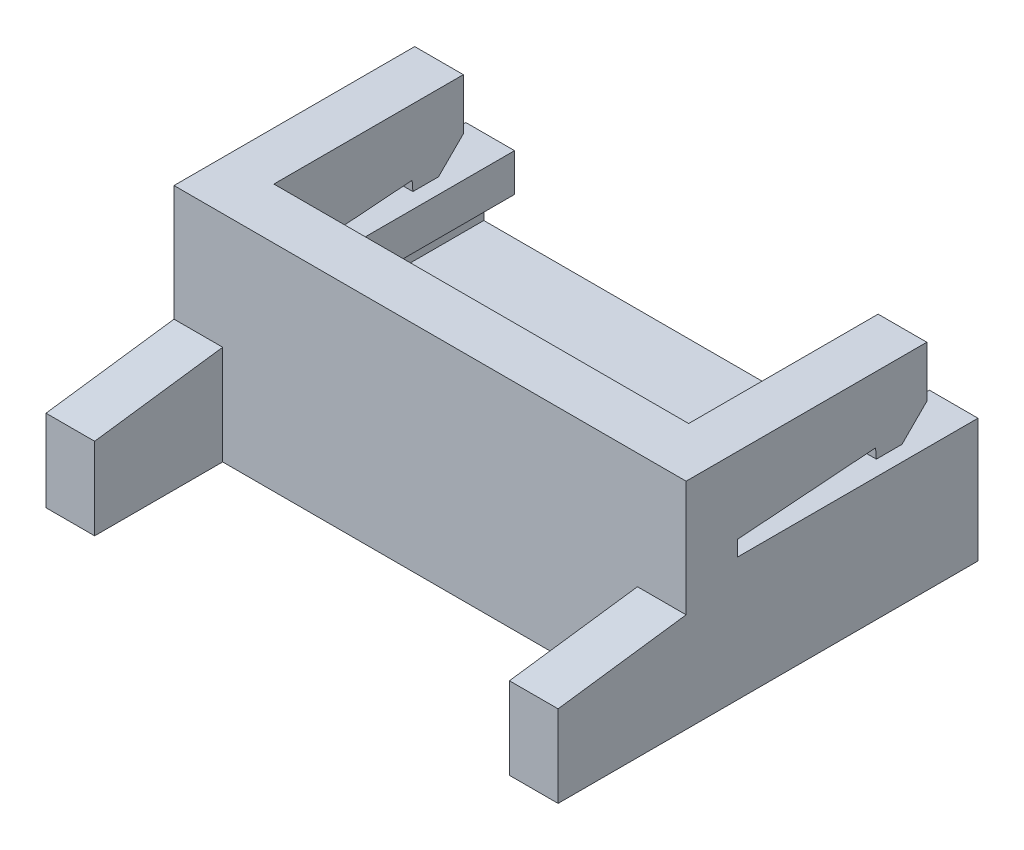
SolidWorks part; units mm, degrees
ref_plane "Front Plane" through (0, 0, 0) normal (0, 0, 1) x (1, 0, 0)
ref_plane "Top Plane" through (0, 0, 0) normal (0, 1, 0) x (1, 0, 0)
ref_plane "Right Plane" through (0, 0, 0) normal (1, 0, 0) x (0, 0, -1)
sketch "Sketch1" plane through (0, 0, 0) normal (0, 1, 0) x (1, 0, 0)
  line L1 (0, 0) -> (10, 0)
  line L2 (0, 0) -> (0, -8.2)
  line L3 (0, -8.2) -> (10, -8.2)
  line L4 (10, 0) -> (10, -8.2)
  dimension "D1" = 8.2
  dimension "D2" = 10
extrude "Boss-Extrude1" add sketch "Sketch1" along normal blind 4.2
sketch "Sketch2" plane through (0, 0, 0) normal (-1, 0, 0) x (0, 0, 1)
  line L0 (8.2, 4.2) -> (8.2, 1.6)
  line L1 (8.2, 4.2) -> (8.2, 0) construction
  line L2 (8.2, 1.6) -> (5.7, 1.94)
  line L3 (5.7, 1.94) -> (5.7, 4.2)
  line L4 (0, 4.2) -> (8.2, 4.2) construction
  line L5 (5.7, 4.2) -> (8.2, 4.2)
  line L6 (0, 0) -> (8.2, 0) construction
  dimension "D1" = 1.6
  dimension "D2" = 2.5
  dimension "D3" = 2.26
extrude "Cut-Extrude1" cut sketch "Sketch2" against normal up to surface (10 mm away) up to face at (10, 2.1, 4.1)
sketch "Sketch3" plane through (0, 0, 0) normal (-1, 0, 0) x (0, 0, 1)
  line L0 (0, 2.4148) -> (4.7, 2.4148)
  line L1 (0, 4.2) -> (0, 0) construction
  line L2 (4.7, 2.4148) -> (4.7, 2.7148)
  line L3 (4.7, 2.7148) -> (2, 2.9148)
  line L4 (2, 2.9148) -> (1.9852, 2.7148)
  line L5 (1.9852, 2.7148) -> (1.4852, 2.7148)
  line L6 (1.4852, 2.7148) -> (1, 3.2)
  line L7 (1, 3.2) -> (1, 4.2)
  line L8 (0, 4.2) -> (5.7, 4.2) construction
  line L9 (1, 4.2) -> (0, 4.2)
  line L10 (0, 4.2) -> (0, 2.4148)
  dimension "D1" = 1
  dimension "D2" = 4.7
  dimension "D3" = 0.3
  dimension "D4" = 0.5
  dimension "D5" = 45
  dimension "D6" = 0.3
  dimension "D7" = 2.7
  dimension "D8" = 0.5
  dimension "D9" = 1
extrude "Cut-Extrude2" cut sketch "Sketch3" against normal up to surface (10 mm away) up to face at (10, 1.99, 4.6333)
sketch "Sketch4" plane through (0, 0, 0) normal (0, 0, -1) x (-1, 0, 0)
  line L0 (-9.65, 0.9335) -> (-9.65, 1.6741)
  line L1 (-9.65, 1.6741) -> (-9.05, 1.6741)
  line L2 (-9.05, 1.6741) -> (-9.05, 4.2)
  line L3 (-10, 4.2) -> (0, 4.2) construction
  line L4 (-9.05, 4.2) -> (-0.95, 4.2)
  line L5 (-0.95, 4.2) -> (-0.95, 1.6741)
  line L6 (-0.95, 1.6741) -> (-0.35, 1.6741)
  line L7 (-0.35, 1.6741) -> (-0.35, 0.9335)
  line L8 (-0.35, 0.9335) -> (-9.65, 0.9335)
  line L9 (-10, 2.4148) -> (-10, 0) construction
  line L10 (0, 2.4148) -> (0, 0) construction
  line L11 (-10, 4.2) -> (-10, 3.2) construction
  line L12 (0, 3.2) -> (0, 4.2) construction
  line L13 (-9.65, 1.6741) -> (-9.65, 2.4148) construction
  line L14 (-10, 2.4148) -> (0, 2.4148) construction
  line L15 (-0.35, 1.6741) -> (-0.35, 2.4148) construction
  point P10 (-10, 1.2074)
  dimension "D1" = 0.35
  dimension "D2" = 0.35
  dimension "D3" = 0.95
  dimension "D4" = 0.95
extrude "Cut-Extrude4" cut sketch "Sketch4" against normal up to surface (4.7 mm away) up to face at (5, 2.5648, 4.7)
sketch "Sketch6" plane through (0, 0, 0) normal (0, -1, 0) x (1, 0, 0)
  line L0 (0, 8.2) -> (10, 8.2) construction
  line L1 (0.95, 8.2) -> (9.05, 8.2)
  line L2 (0.95, 8.2) -> (0.95, 5.7)
  line L3 (0.95, 5.7) -> (9.05, 5.7)
  line L4 (9.05, 8.2) -> (9.05, 5.7)
  line L5 (0.95, 4.7) -> (0.95, 1) construction
  line L6 (9.05, 4.7) -> (9.05, 1) construction
  line L7 (10, 5.7) -> (0, 5.7) construction
extrude "Cut-Extrude5" cut sketch "Sketch6" against normal up to surface (1.6 mm away)
